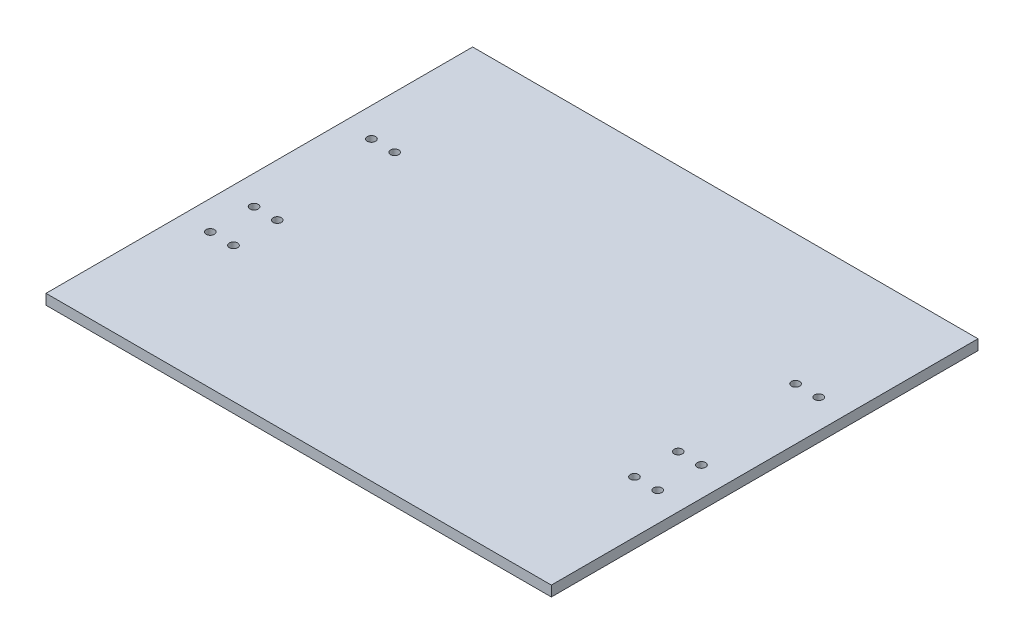
SolidWorks part; units mm, degrees
material "Custom Plastic"
ref_plane "Front Plane" through (0, 0, 0) normal (0, 0, 1) x (1, 0, 0)
ref_plane "Top Plane" through (0, 0, 0) normal (0, 1, 0) x (1, 0, 0)
ref_plane "Right Plane" through (0, 0, 0) normal (1, 0, 0) x (0, 0, -1)
sketch "Sketch1" plane through (0, 0, 0) normal (0, 1, 0) x (1, 0, 0)
  line L1 (-59.5, -51.5) -> (59.5, -51.5)
  line L2 (-59.5, -51.5) -> (-59.5, 51.5)
  line L3 (-59.5, 51.5) -> (59.5, 51.5)
  line L4 (59.5, -51.5) -> (59.5, 51.5)
  line L5 (-59.5, -51.5) -> (59.5, 51.5) construction
  line L6 (-59.5, 51.5) -> (59.5, -51.5) construction
  point P0 (0, 0)
  dimension "D1" = 119
  dimension "D2" = 103
extrude "Boss-Extrude1" add sketch "Sketch1" along normal blind 2.5
sketch "Sketch2" plane through (0, 0, 0) normal (0, -1, 0) x (1, 0, 0)
  line L0 (-59.5, 51.5) -> (59.5, 51.5) construction
  line L1 (-59.5, -51.5) -> (-59.5, 51.5) construction
  line L2 (0, 51.5) -> (0, -51.5) construction
  line L3 (59.5, -51.5) -> (-59.5, -51.5) construction
  line L4 (-48.4, 51.5) -> (-48.4, -51.5) construction
  circle A0 centre (-54, -20.06) radius 1
  circle A1 centre (-54, 8.27) radius 1
  circle A2 centre (-54, 18.84) radius 1
  circle A3 centre (54, -20.06) radius 1
  circle A4 centre (54, 8.27) radius 1
  circle A5 centre (54, 18.84) radius 1
  circle A6 centre (-48.4, 18.84) radius 1
  circle A7 centre (-48.4, -20.06) radius 1
  circle A8 centre (-48.4, 8.27) radius 1
  circle A9 centre (48.4, -20.06) radius 1
  circle A10 centre (48.4, 8.27) radius 1
  circle A11 centre (48.4, 18.84) radius 1
  dimension "D7" = 2
  dimension "D8" = 2
  dimension "D9" = 2
  dimension "D12" = 2
  dimension "D14" = 2
  dimension "D15" = 43.23
  dimension "D16" = 2
  dimension "D1" = 32.66
  dimension "D2" = 43.23
  dimension "D3" = 71.56
  dimension "D4" = 5.5
  dimension "D5" = 5.5
  dimension "D6" = 5.5
  dimension "D10" = 11.1
  dimension "D11" = 32.66
  dimension "D13" = 71.56
extrude "Cut-Extrude1" cut sketch "Sketch2" against normal blind 10
sketch "Sketch3" plane through (-59.5, 0, 0) normal (-1, 0, 0) x (0, 0, 1)
  line L8 (-51.5, 0) -> (51.5, 0)
  line L9 (51.5, 0) -> (51.5, 2.5)
  line L10 (51.5, 2.5) -> (-51.5, 2.5)
  line L11 (-51.5, 2.5) -> (-51.5, 0)
  line L12 (-51.5, 0) -> (51.5, 0)
  line L13 (51.5, 0) -> (51.5, 2.5)
  line L14 (51.5, 2.5) -> (-51.5, 2.5)
  line L15 (-51.5, 2.5) -> (-51.5, 0)
  dimension "D1" = 0
extrude "Boss-Extrude2" add sketch "Sketch3" along normal blind 1.5
sketch "Sketch4" plane through (59.5, 0, 0) normal (1, 0, 0) x (0, 0, -1)
  line L4 (-51.5, 0) -> (51.5, 0)
  line L5 (51.5, 0) -> (51.5, 2.5)
  line L6 (51.5, 2.5) -> (-51.5, 2.5)
  line L7 (-51.5, 2.5) -> (-51.5, 0)
  line L8 (-51.5, 0) -> (51.5, 0)
  line L9 (51.5, 0) -> (51.5, 2.5)
  line L10 (51.5, 2.5) -> (-51.5, 2.5)
  line L11 (-51.5, 2.5) -> (-51.5, 0)
  dimension "D1" = 0
extrude "Boss-Extrude3" add sketch "Sketch4" along normal blind 1.5
